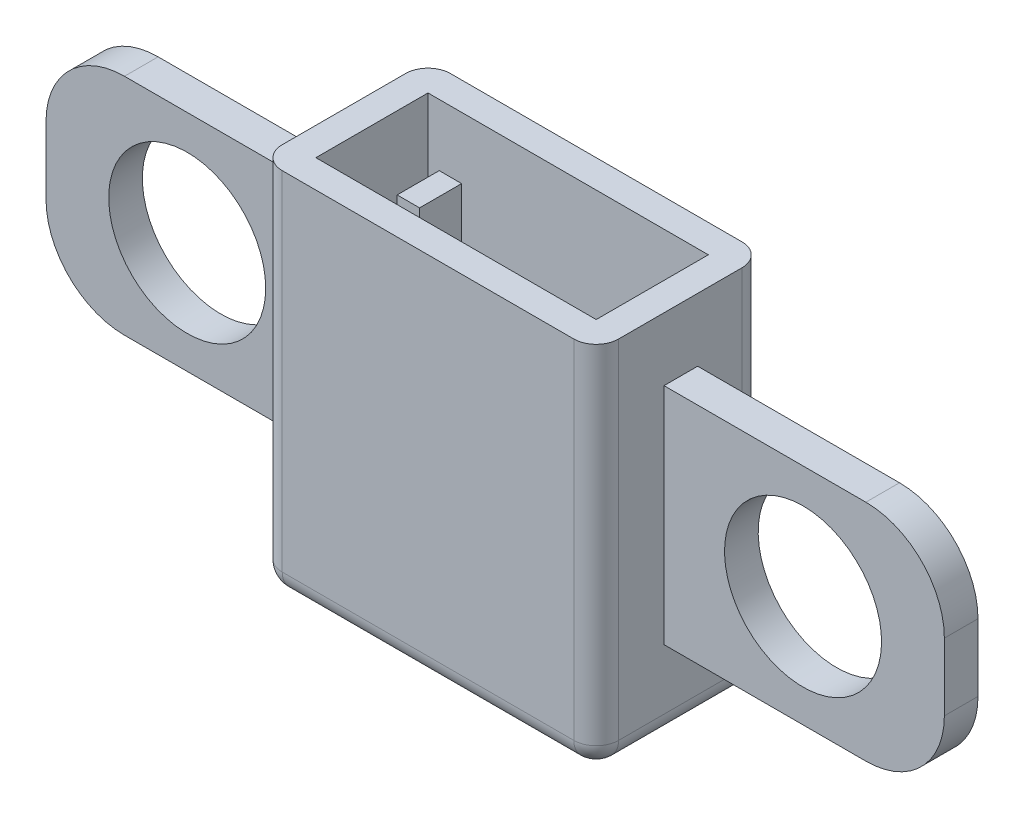
SolidWorks part; units mm, degrees
ref_plane "Front Plane" through (0, 0, 0) normal (0, 0, 1) x (1, 0, 0)
ref_plane "Top Plane" through (0, 0, 0) normal (0, 1, 0) x (1, 0, 0)
ref_plane "Right Plane" through (0, 0, 0) normal (1, 0, 0) x (0, 0, -1)
sketch "Sketch1" plane through (0, 0, 0) normal (0, 1, 0) x (1, 0, 0)
  line L1 (-15, 7.5) -> (15, 7.5)
  line L2 (-15, 7.5) -> (-15, -7.5)
  line L3 (-15, -7.5) -> (15, -7.5)
  line L4 (15, 7.5) -> (15, -7.5)
  line L5 (-15, 7.5) -> (15, -7.5) construction
  line L6 (-15, -7.5) -> (15, 7.5) construction
  point P0 (0, 0)
  dimension "D1" = 30
  dimension "D2" = 15
extrude "Boss-Extrude1" add sketch "Sketch1" along normal blind 33
sketch "Sketch2" plane through (0, 33, 0) normal (0, 1, 0) x (1, 0, 0)
  line L8 (12.5, -5) -> (12.5, 5)
  line L9 (12.5, 5) -> (-12.5, 5)
  line L10 (-12.5, 5) -> (-12.5, -5)
  line L11 (-12.5, -5) -> (12.5, -5)
  line L12 (12.5, -5) -> (12.5, 5)
  line L13 (12.5, 5) -> (-12.5, 5)
  line L14 (-12.5, 5) -> (-12.5, -5)
  line L15 (-12.5, -5) -> (12.5, -5)
  dimension "D1" = 2.5
extrude "Cut-Extrude1" cut sketch "Sketch2" against normal blind 30.5
sketch "Sketch3" plane through (0, 2.5, 0) normal (0, 1, 0) x (1, 0, 0)
  line L1 (-11.5, 1.25) -> (11.5, 1.25)
  line L2 (-11.5, 1.25) -> (-11.5, -1.25)
  line L3 (-11.5, -1.25) -> (11.5, -1.25)
  line L4 (11.5, 1.25) -> (11.5, -1.25)
  line L5 (-11.5, 1.25) -> (11.5, -1.25) construction
  line L6 (-11.5, -1.25) -> (11.5, 1.25) construction
  point P0 (0, 0)
  dimension "D1" = 23
  dimension "D2" = 2.5
extrude "Cut-Extrude2" cut sketch "Sketch3" against normal blind 30.5
sketch "Sketch4" plane through (0, 2.5, 0) normal (0, 1, 0) x (1, 0, 0)
  line L0 (-12.5, -5) -> (12.5, -5) construction
  line L1 (-11.5, -1.25) -> (-9.5, -1.25)
  line L2 (-11.5, -1.25) -> (-11.5, -5)
  line L3 (-11.5, -5) -> (-9.5, -5)
  line L4 (-9.5, -1.25) -> (-9.5, -5)
  dimension "D1" = 2
extrude "Boss-Extrude2" add sketch "Sketch4" along normal blind 25
sketch "Sketch5" plane through (0, 2.5, 0) normal (0, 1, 0) x (1, 0, 0)
  line L0 (-9.5, -5) -> (12.5, -5) construction
  line L1 (11.5, -1.25) -> (9.5, -1.25)
  line L2 (11.5, -1.25) -> (11.5, -5)
  line L3 (11.5, -5) -> (9.5, -5)
  line L4 (9.5, -1.25) -> (9.5, -5)
  dimension "D1" = 2
extrude "Boss-Extrude3" add sketch "Sketch5" along normal blind 25
sketch "Sketch6" plane through (0, 2.5, 0) normal (0, 1, 0) x (1, 0, 0)
  line L0 (12.5, 5) -> (-12.5, 5) construction
  line L1 (-11.5, 1.25) -> (-9.5, 1.25)
  line L2 (-11.5, 1.25) -> (-11.5, 5)
  line L3 (-11.5, 5) -> (-9.5, 5)
  line L4 (-9.5, 1.25) -> (-9.5, 5)
  dimension "D1" = 2
extrude "Boss-Extrude4" add sketch "Sketch6" along normal blind 25
sketch "Sketch7" plane through (0, 2.5, 0) normal (0, 1, 0) x (1, 0, 0)
  line L0 (12.5, 5) -> (-9.5, 5) construction
  line L1 (11.5, 1.25) -> (9.5, 1.25)
  line L2 (11.5, 1.25) -> (11.5, 5)
  line L3 (11.5, 5) -> (9.5, 5)
  line L4 (9.5, 1.25) -> (9.5, 5)
  dimension "D1" = 2
extrude "Boss-Extrude5" add sketch "Sketch7" along normal blind 25
fillet "Fillet1" radius 2 8 edges at (-15, 0, 0) (0, 0, 7.5) (15, 0, 0) (0, 0, -7.5) (15, 16.5, -7.5) (-15, 16.5, -7.5) (15, 16.5, 7.5) (-15, 16.5, 7.5)
sketch "Sketch8" plane through (-15, 0, 0) normal (-1, 0, 0) x (0, 0, 1)
  line L0 (-5.5, 33) -> (5.5, 2)
  line L2 (-1.4361, 27.3198) -> (1.5639, 27.3198)
  line L3 (-1.4361, 27.3198) -> (-1.4361, 7.3198)
  line L4 (-1.4361, 7.3198) -> (1.5639, 7.3198)
  line L5 (1.5639, 27.3198) -> (1.5639, 7.3198)
  line L6 (-1.4361, 27.3198) -> (1.5639, 7.3198) construction
  line L7 (-1.4361, 7.3198) -> (1.5639, 27.3198) construction
  point P5 (0.0639, 17.3198)
  dimension "D1" = 20
  dimension "D2" = 3
extrude "Boss-Extrude6" add sketch "Sketch8" along normal blind 25 contours L5 L0 L3 L4 | L5 L2 L3 L0
sketch "Sketch9" plane through (0, 0, 1.5639) normal (0, 0, 1) x (1, 0, 0)
  line L0 (-40, 27.3198) -> (-15, 7.3198)
  circle A0 centre (-27.4092, 17.2472) radius 7
  dimension "D1" = 14
extrude "Cut-Extrude3" cut sketch "Sketch9" against normal blind 25 contours L0 A0 | L0 A0
fillet "Fillet2" radius 7 1 edges at (-40, 7.3198, 0.0639)
fillet "Fillet3" radius 7 1 edges at (-40, 27.3198, 0.0639)
sketch "Sketch10" plane through (15, 0, 0) normal (1, 0, 0) x (0, 0, -1)
  line L0 (-5.5, 33) -> (5.5, 2)
  line L2 (-1.4546, 27.3722) -> (1.5454, 27.3722)
  line L3 (-1.4546, 27.3722) -> (-1.4546, 7.3722)
  line L4 (-1.4546, 7.3722) -> (1.5454, 7.3722)
  line L5 (1.5454, 27.3722) -> (1.5454, 7.3722)
  line L6 (-1.4546, 27.3722) -> (1.5454, 7.3722) construction
  line L7 (-1.4546, 7.3722) -> (1.5454, 27.3722) construction
  point P5 (0.0454, 17.3722)
  dimension "D1" = 20
  dimension "D2" = 3
extrude "Boss-Extrude7" add sketch "Sketch10" along normal blind 25 contours L5 L0 L3 L4 | L5 L2 L3 L0
sketch "Sketch11" plane through (0, 0, -1.5454) normal (0, 0, -1) x (-1, 0, 0)
  line L0 (-40, 27.3722) -> (-15, 7.3722)
  circle A0 centre (-27.3972, 17.2899) radius 7
extrude "Cut-Extrude4" cut sketch "Sketch11" against normal blind 25 contours L0 A0 | L0 A0
fillet "Fillet4" radius 7 2 edges at (40, 7.3722, -0.0454) (40, 27.3722, -0.0454)
